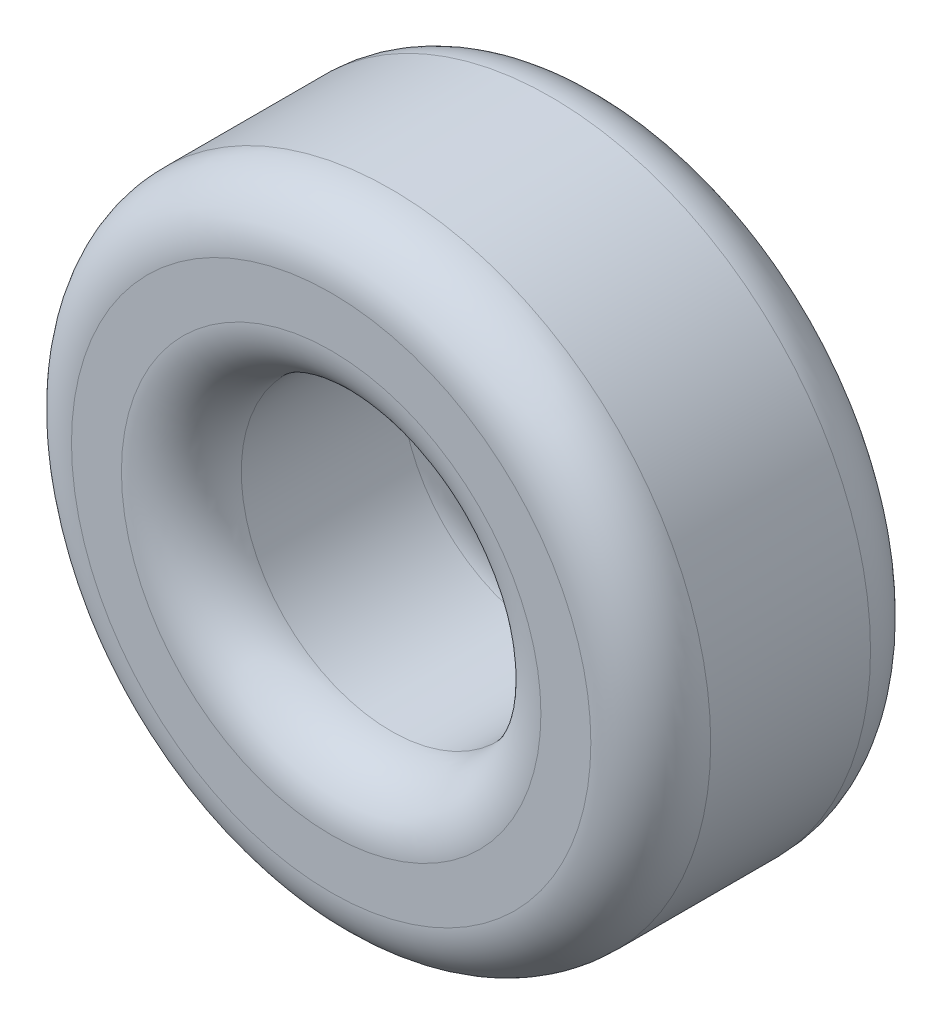
SolidWorks part; units mm, degrees
ref_plane "Front Plane" through (0, 0, 0) normal (0, 0, 1) x (1, 0, 0)
ref_plane "Top Plane" through (0, 0, 0) normal (0, 1, 0) x (1, 0, 0)
ref_plane "Right Plane" through (0, 0, 0) normal (1, 0, 0) x (0, 0, -1)
sketch "Sketch1" plane through (0, 0, 0) normal (0, 0, 1) x (1, 0, 0)
  circle A0 centre (0, 0) radius 0.75
  circle A1 centre (0, 0) radius 1.6
  dimension "D1" = 1.5
  dimension "D2" = 3.2
extrude "Boss-Extrude1" add sketch "Sketch1" along normal mid plane 1.4
fillet "Fillet2" radius 0.3 4 edges at (0.75, 0, -0.7) (1.6, 0, -0.7) (0.75, 0, 0.7) (1.6, 0, 0.7)
